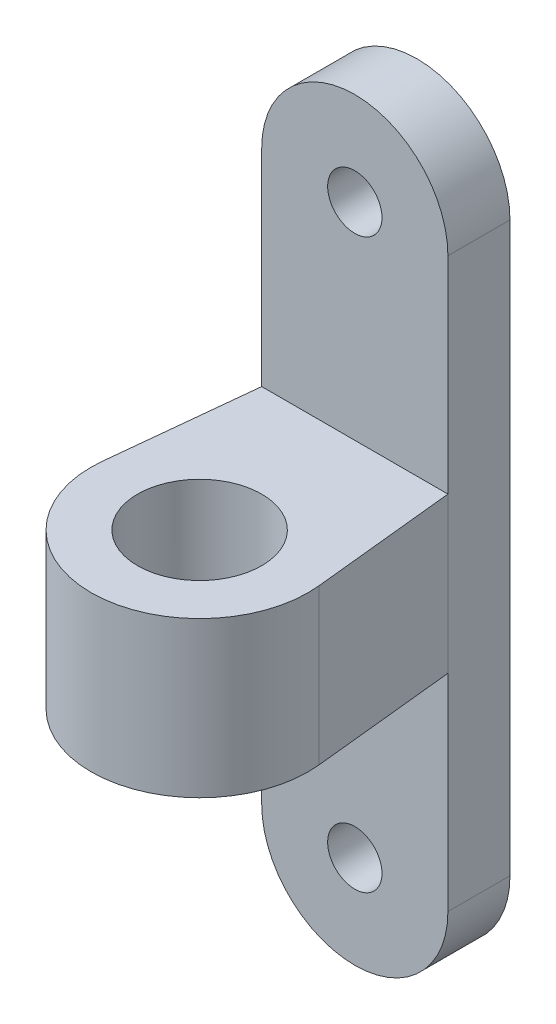
SolidWorks part; units mm, degrees
material "ABS"
ref_plane "Plano frontal" through (0, 0, 0) normal (0, 0, 1) x (1, 0, 0)
ref_plane "Plano superior" through (0, 0, 0) normal (0, 1, 0) x (1, 0, 0)
ref_plane "Plano direito" through (0, 0, 0) normal (1, 0, 0) x (0, 0, -1)
sketch "Esboço1" plane through (0, 0, 0) normal (0, 0, 1) x (1, 0, 0)
  line L0 (0, 0) -> (0, 36.6) construction
  line L1 (-6, 0) -> (-6, 36.6)
  line L2 (6, 0) -> (6, 36.6)
  circle A0 centre (0, 0) radius 1.75
  circle A1 centre (0, 36.6) radius 1.75
  arc A2 (-6, 0) -> (6, 0) centre (0, 0) ccw
  arc A3 (6, 36.6) -> (-6, 36.6) centre (0, 36.6) ccw
  point P5 (0, 18.3)
  dimension "D1" = 36.6
  dimension "D2" = 3.5
  dimension "D3" = 6
extrude "Ressalto-extrusão1" add sketch "Esboço1" along normal blind 4
sketch "Esboço2" plane through (0, 0, 0) normal (0, 0, -1) x (-1, 0, 0)
  line L0 (0, 36.6) -> (0, 0) construction
  line L2 (16.4836, 23.3) -> (-16.4836, 23.3)
  line L3 (16.4836, 23.3) -> (16.4836, 13.3)
  line L4 (16.4836, 13.3) -> (-16.4836, 13.3)
  line L5 (-16.4836, 23.3) -> (-16.4836, 13.3)
  line L6 (16.4836, 23.3) -> (-16.4836, 13.3) construction
  line L7 (16.4836, 13.3) -> (-16.4836, 23.3) construction
  point P4 (0, 18.3)
  dimension "D1" = 10
extrude "Ressalto-extrusão2" add sketch "Esboço2" against normal blind 25
sketch "Esboço3" plane through (0, 23.3, 0) normal (0, 1, 0) x (1, 0, 0)
  line L0 (-6, -4) -> (-6.9626, -13.2776)
  line L3 (0, 0) -> (0, -17.438) construction
  line L4 (-6, -4) -> (-6, 0)
  line L5 (6, -4) -> (-6, -4) construction
  line L6 (6, -4) -> (6.9626, -13.2776)
  line L7 (-6, 0) -> (-6, -4) construction
  line L8 (-16.4836, 0) -> (-6, 0) construction
  line L9 (-6, 0) -> (6, 0)
  line L10 (6, 0) -> (6, -4)
  circle A0 centre (0, -14) radius 4
  arc A1 (-6.9626, -13.2776) -> (6.9626, -13.2776) centre (0, -14) ccw
  point P7 (0, -4)
  dimension "D1" = 4
  dimension "D3" = 7
extrude "Corte-extrusão3" cut sketch "Esboço3" against normal through all
